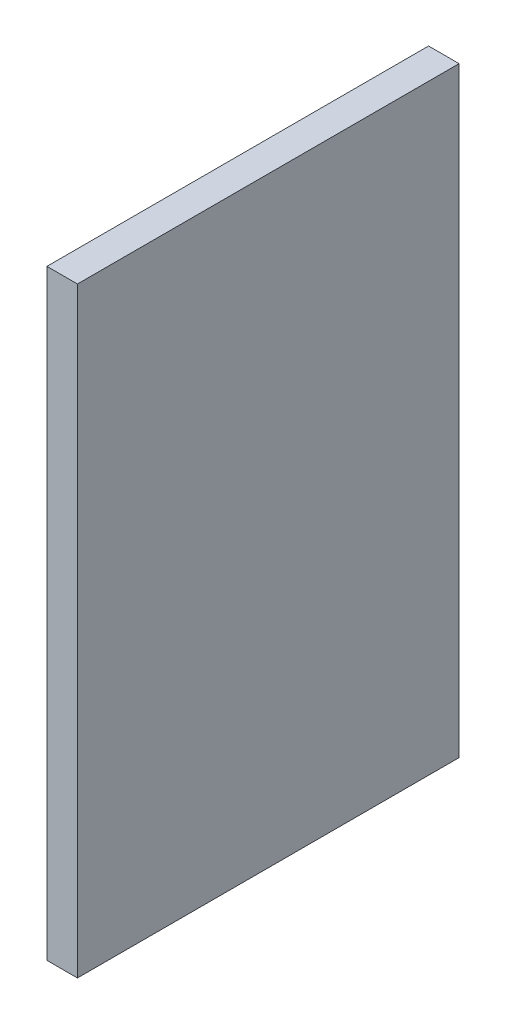
SolidWorks part; units mm, degrees
ref_plane "Front" through (0, 0, 0) normal (0, 0, 1) x (1, 0, 0)
ref_plane "Top" through (0, 0, 0) normal (0, 1, 0) x (1, 0, 0)
ref_plane "Right" through (0, 0, 0) normal (1, 0, 0) x (0, 0, -1)
sketch "Sketch1" plane through (0, 0, 0) normal (0, 1, 0) x (1, 0, 0)
  line L1 (0, 0) -> (2.54, 0)
  line L2 (0, 0) -> (0, 31.75)
  line L3 (0, 31.75) -> (2.54, 31.75)
  line L4 (2.54, 0) -> (2.54, 31.75)
  line L5 (0, 0) -> (2.54, 31.75) construction
  line L6 (0, 31.75) -> (2.54, 0) construction
  point P4 (1.27, 15.875)
  dimension "D1" = 31.75
  dimension "D2" = 2.54
extrude "Boss-Extrude1" add sketch "Sketch1" along normal blind 49.9999
sketch "Sketch5" plane through (0, 0, 0) normal (1, 0, 0) x (0, 0, -1)
  line L0 (15.875, 0) -> (15.875, 15.0012) construction
  line L1 (31.75, 0) -> (0, 0) construction
  circle A0 centre (15.875, 15.0012) radius 2.9997
  circle A1 centre (15.875, 15.0012) radius 1.6002
  circle A2 centre (15.875, 35.0012) radius 1.6002
  circle A3 centre (15.875, 35.0012) radius 2.9997
  dimension "D2" = 5.9995
  dimension "D3" = 3.2004
  dimension "D1" = 15.0012
  dimension "D4" = 20
extrude "Boss-Extrude3" add sketch "Sketch5" against normal blind 8.6106
